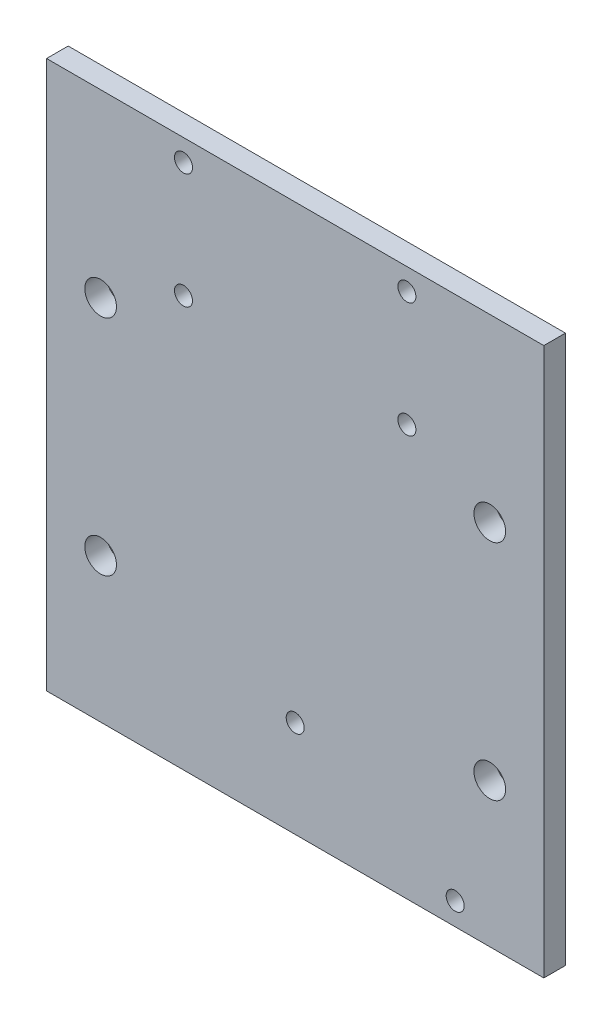
SolidWorks part; units mm, degrees
ref_plane "正面" through (0, 0, 0) normal (0, 0, 1) x (1, 0, 0)
ref_plane "平面" through (0, 0, 0) normal (0, 1, 0) x (1, 0, 0)
ref_plane "右側面" through (0, 0, 0) normal (1, 0, 0) x (0, 0, -1)
sketch "ｽｹｯﾁ1" plane through (0, 0, 0) normal (0, 0, 1) x (1, 0, 0)
  line L1 (-34.5, 43) -> (34.5, 43)
  line L2 (-34.5, 43) -> (-34.5, -43)
  line L3 (-34.5, -43) -> (34.5, -43)
  line L4 (34.5, 43) -> (34.5, -43)
  line L5 (-34.5, 43) -> (34.5, -43) construction
  line L6 (-34.5, -43) -> (34.5, 43) construction
  line L7 (34.5, -43) -> (27, -43)
  line L8 (34.5, -43) -> (34.5, -33)
  line L9 (34.5, -33) -> (27, -33)
  line L10 (27, -43) -> (27, -33)
  line L11 (-34.5, -43) -> (-27, -43)
  line L12 (-34.5, -43) -> (-34.5, -33)
  line L13 (-34.5, -33) -> (-27, -33)
  line L14 (-27, -43) -> (-27, -33)
  line L15 (-34.5, 43) -> (-27, 43)
  line L16 (-34.5, 43) -> (-34.5, 33.6522)
  line L17 (-34.5, 33.6522) -> (-27, 33.6522)
  line L18 (-27, 43) -> (-27, 33.6522)
  line L19 (34.5, 43) -> (27, 43)
  line L20 (34.5, 43) -> (34.5, 33.6522)
  line L21 (34.5, 33.6522) -> (27, 33.6522)
  line L22 (27, 43) -> (27, 33.6522)
  point P0 (0, 0)
  dimension "D1" = 86
  dimension "D2" = 69
  dimension "D3" = 7.5
  dimension "D4" = 10
  dimension "D5" = 7.5
  dimension "D6" = 7.5
  dimension "D7" = 7.5
  dimension "D8" = 10
extrude "ﾎﾞｽ - 押し出し1" add sketch "ｽｹｯﾁ1" along normal blind 3 contours L22 L1 L18 L17 L2 L13 L14 L3 L10 L9 L4 L21 | L18 L1 L2 L17 | L1 L22 L21 L4 | L10 L3 L4 L9 | L3 L14 L13 L2
sketch "ｽｹｯﾁ2" plane through (0, 0, 3) normal (0, 0, 1) x (1, 0, 0)
  line L0 (27, -43) -> (27, -24)
  line L1 (-34.5, 43) -> (-27, 43)
  line L2 (-34.5, 43) -> (-34.5, 18)
  line L3 (-34.5, 18) -> (-27, 18)
  line L4 (-27, 43) -> (-27, 18)
  line L5 (34.5, 43) -> (27, 43)
  line L6 (34.5, 43) -> (34.5, 18)
  line L7 (34.5, 18) -> (27, 18)
  line L8 (27, 43) -> (27, 18)
  line L9 (-34.5, -43) -> (-27, -43)
  line L10 (-34.5, -43) -> (-34.5, -13)
  line L11 (-34.5, -13) -> (-27, -13)
  line L12 (-27, -43) -> (-27, -13)
  line L13 (34.5, -43) -> (27, -43)
  line L14 (34.5, -43) -> (34.5, -13)
  line L15 (34.5, -13) -> (27, -13)
  line L16 (27, -43) -> (27, -13)
  line L20 (-34.5, 43) -> (-34.5, 40)
  line L21 (-34.5, 40) -> (-15.5, 40)
  line L22 (34.5, 43) -> (34.5, 40)
  line L23 (34.5, 40) -> (15.5, 40)
  circle A0 centre (-27, 18) radius 2.2
  circle A1 centre (27, 18) radius 2.2
  circle A2 centre (27, -13) radius 2.2
  circle A3 centre (-27, -13) radius 2.2
  circle A7 centre (-15.5, 40) radius 1.6
  circle A8 centre (15.5, 40) radius 1.6
  dimension "D9" = 4.4
  dimension "D10" = 4.4
  dimension "D11" = 4.4
  dimension "D12" = 4.4
  dimension "D21" = 3.2
  dimension "D24" = 3.2
  dimension "D1" = 7.5
  dimension "D2" = 7.5
  dimension "D3" = 7.5
  dimension "D4" = 7.5
  dimension "D5" = 30
  dimension "D6" = 30
  dimension "D7" = 25
  dimension "D8" = 25
  dimension "D20" = 3
  dimension "D22" = 19
  dimension "D23" = 3
  dimension "D25" = 19
extrude "ｶｯﾄ - 押し出し1" cut sketch "ｽｹｯﾁ2" against normal through all contours L3 A0 L4 | L4 A0 L3 | L7 A1 L8 | L8 A1 L7
sketch "ｽｹｯﾁ4" plane through (0, 0, 3) normal (0, 0, 1) x (1, 0, 0)
  line L0 (-15.5, 40) -> (-15.5, 24)
  line L1 (15.5, 40) -> (15.5, 24)
  circle A0 centre (-15.5, 24) radius 1.6
  circle A1 centre (15.5, 24) radius 1.6
  dimension "D3" = 3.2
  dimension "D4" = 3.2
  dimension "D1" = 16
  dimension "D2" = 16
hole_wizard "M3x0.5 ねじ穴1" positions "3Dｽｹｯﾁ1" profile "ｽｹｯﾁ5" tap size "M3x0.5" standard "JIS"
sketch3d "3Dｽｹｯﾁ1"
  point P0 (-15.5, 24, 3)
  point P3 (15.5, 24, 3)
  point P6 (-15.5, 40, 3)
  point P9 (15.5, 40, 3)
sketch "ｽｹｯﾁ5" plane through (-15.5, 24, 3) normal (1, 0, 0) x (0, -1, 0)
  line L0 (0, 0) -> (0, 9.2511)
  line L1 (0, 9.2511) -> (1.25, 8.5)
  line L2 (1.25, 8.5) -> (1.25, 0)
  line L5 (1.25, 0) -> (0, 0)
  line L10 (0, 9.2511) -> (-1.25, 8.5) construction
  line L11 (0, -6.35) -> (0, 107.95) construction
  dimension "ねじ下穴ﾄﾞﾘﾙ直径" = 2.5
  dimension "ねじ下穴ﾄﾞﾘﾙの深さ" = 8.5
  dimension "ﾄﾞﾘﾙ角度" = 118
cosmetic thread "穴のねじ山1" parameters "D1"=3, "D2"=3
cosmetic thread "穴のねじ山2" parameters "D1"=3, "D2"=3
cosmetic thread "穴のねじ山3" parameters "D1"=3, "D2"=3
cosmetic thread "穴のねじ山4" parameters "D1"=3, "D2"=3
sketch "ｽｹｯﾁ6" plane through (0, -43, 0) normal (0, -1, 0) x (-1, 0, 0)
  line L0 (34.5, -3) -> (34.5, 0) construction
  line L1 (-34.5, -3) -> (34.5, -3)
  line L2 (-34.5, -3) -> (-34.5, 0)
  line L3 (-34.5, 0) -> (34.5, 0)
  line L4 (34.5, -3) -> (34.5, 0)
  line L5 (34.5, 0) -> (-34.5, 0) construction
extrude "ｶｯﾄ - 押し出し2" cut sketch "ｽｹｯﾁ6" against normal blind 20
sketch "ｽｹｯﾁ7" plane through (0, -23, 0) normal (0, -1, 0) x (-1, 0, 0)
  line L1 (-34.5, -3) -> (34.5, -3)
  line L2 (-34.5, -3) -> (-34.5, 0)
  line L3 (-34.5, 0) -> (34.5, 0)
  line L4 (34.5, -3) -> (34.5, 0)
extrude "ﾎﾞｽ - 押し出し2" add sketch "ｽｹｯﾁ7" along normal blind 10
sketch "ｽｹｯﾁ8" plane through (0, 0, 3) normal (0, 0, 1) x (1, 0, 0)
  line L0 (0, -33) -> (0, -19.5746)
  line L1 (34.5, -33) -> (-34.5, -33) construction
  line L2 (0, -19.5746) -> (22.2, -19.5746)
  line L3 (22.2, -19.5746) -> (22.2, -29.8746)
  circle A0 centre (22.2, -29.8746) radius 2.6122
  circle A1 centre (0, -19.5746) radius 1.8231
  dimension "D1" = 22.2
  dimension "D2" = 10.3
hole_wizard "M3x0.5 ねじ穴2" positions "3Dｽｹｯﾁ2" profile "ｽｹｯﾁ9" tap size "M3x0.5" standard "JIS"
sketch3d "3Dｽｹｯﾁ2"
  point P0 (0, -19.5746, 3)
  point P3 (22.2, -29.8746, 3)
sketch "ｽｹｯﾁ9" plane through (0, -19.5746, 3) normal (1, 0, 0) x (0, -1, 0)
  line L0 (0, 0) -> (0, 9.2511)
  line L1 (0, 9.2511) -> (1.25, 8.5)
  line L2 (1.25, 8.5) -> (1.25, 0)
  line L5 (1.25, 0) -> (0, 0)
  line L10 (0, 9.2511) -> (-1.25, 8.5) construction
  line L11 (0, -6.35) -> (0, 107.95) construction
  dimension "ねじ下穴ﾄﾞﾘﾙ直径" = 2.5
  dimension "ねじ下穴ﾄﾞﾘﾙの深さ" = 8.5
  dimension "ﾄﾞﾘﾙ角度" = 118
cosmetic thread "穴のねじ山5" parameters "D1"=3, "D2"=3
cosmetic thread "穴のねじ山6" parameters "D1"=3, "D2"=3
